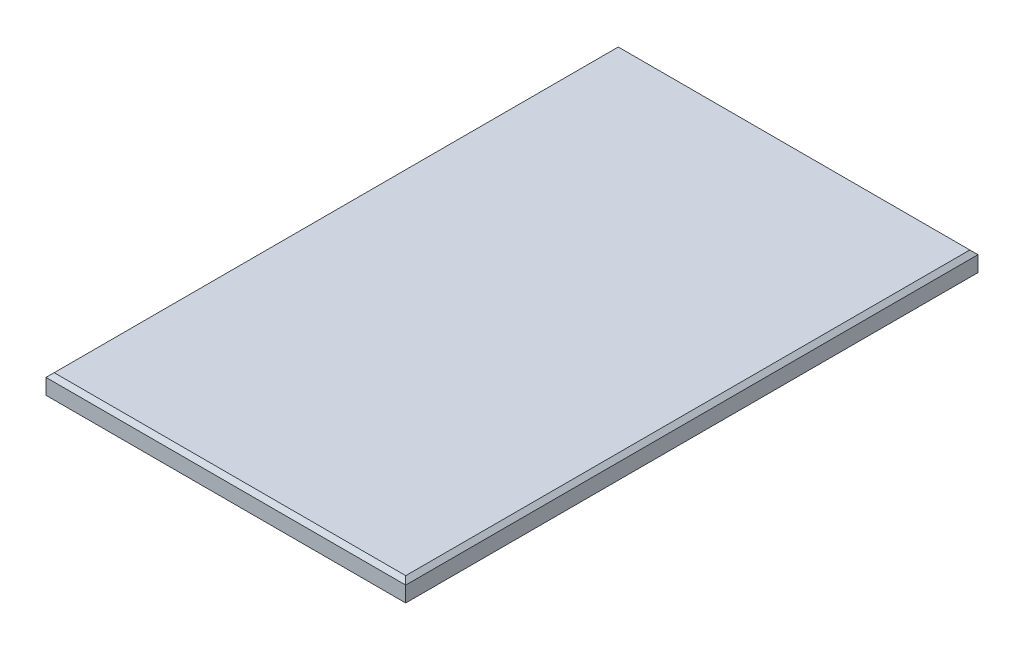
SolidWorks part; units mm, degrees
ref_plane "Front Plane" through (0, 0, 0) normal (0, 0, 1) x (1, 0, 0)
ref_plane "Top Plane" through (0, 0, 0) normal (0, 1, 0) x (1, 0, 0)
ref_plane "Right Plane" through (0, 0, 0) normal (1, 0, 0) x (0, 0, -1)
sketch "Sketch1" plane through (0, 0, 0) normal (0, 1, 0) x (1, 0, 0)
  line L1 (0, 0) -> (22, 0)
  line L2 (0, 0) -> (0, 35)
  line L3 (0, 35) -> (22, 35)
  line L4 (22, 0) -> (22, 35)
  dimension "D1" = 35
  dimension "D2" = 22
extrude "Boss-Extrude1" add sketch "Sketch1" along normal blind 1.2
chamfer "Chamfer1" distance 0.25 angle 45 4 edges at (22, 1.2, -17.5) (11, 1.2, 0) (0, 1.2, -17.5) (11, 1.2, -35)
